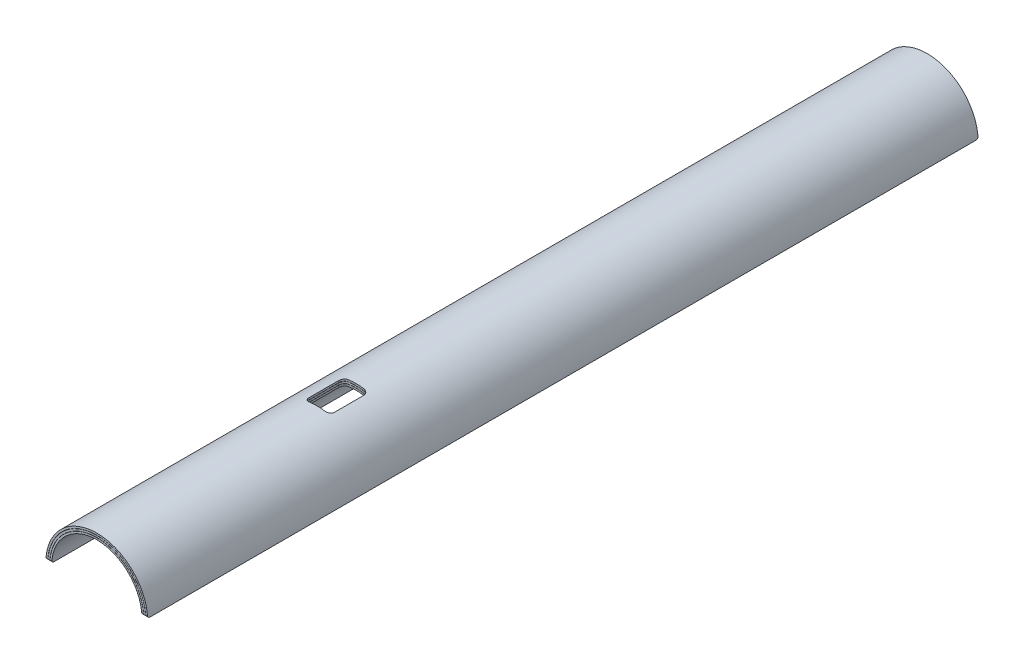
SolidWorks part; units mm, degrees
material "insulation"
ref_plane "Front Plane" through (0, 0, 0) normal (0, 0, 1) x (1, 0, 0)
ref_plane "Top Plane" through (0, 0, 0) normal (0, 1, 0) x (1, 0, 0)
ref_plane "Right Plane" through (0, 0, 0) normal (1, 0, 0) x (0, 0, -1)
sketch "Sketch1" plane through (0, 0, 0) normal (0, 0, 1) x (1, 0, 0)
  line L0 (-56.921, 3) -> (56.921, 3) construction
  line L1 (0, 0) -> (39.4027, 0) construction
  arc A0 (56.921, 3) -> (-56.921, 3) centre (0, 0) ccw
  dimension "D1" = 3
  dimension "D2" = 57
extrude "Extrude-Thin1" add sketch "Sketch1" along normal mid plane 1048 thin
sketch "Sketch2" plane through (0, 0, 0) normal (0, 0, 1) x (1, 0, 0)
  line L0 (-59.4443, 3) -> (59.4443, 3) construction
  line L1 (-56.921, 3) -> (56.921, 3) construction
  arc A0 (59.4443, 3) -> (-59.4443, 3) centre (0, 0) ccw
  dimension "D1" = 59.52
extrude "Extrude-Thin2" add sketch "Sketch2" along normal mid plane 1048 separate body thin
sketch "Sketch3" plane through (0, 0, 0) normal (0, 0, 1) x (1, 0, 0)
  line L0 (-61.9674, 3) -> (61.9674, 3) construction
  line L1 (-56.921, 3) -> (56.921, 3) construction
  arc A0 (61.9674, 3) -> (-61.9674, 3) centre (0, 0) ccw
  dimension "D1" = 62.04
extrude "Extrude-Thin3" add sketch "Sketch3" along normal mid plane 1048 separate body thin
fillet "Fillet1" radius 3 4 edges at (63.1161, 3.0556, 524) (63.1161, 3.0556, -524) (-63.1161, 3.0556, -524) (-63.1161, 3.0556, 524)
fillet "Fillet2" radius 3 4 edges at (60.5929, 3.058, -524) (-60.5929, 3.058, -524) (60.5929, 3.058, 524) (-60.5929, 3.058, 524)
fillet "Fillet3" radius 3 4 edges at (58.0694, 3.0605, 524) (-58.0694, 3.0605, 524) (58.0694, 3.0605, -524) (-58.0694, 3.0605, -524)
sketch "Sketch4" plane through (0, 0, 0) normal (0, 1, 0) x (1, 0, 0)
  line L0 (0, 0) -> (0, 89.1347) construction
  line L1 (9.9984, -246) -> (-9.9984, -246)
  line L2 (16, -239.9984) -> (16, -203.0016)
  line L3 (9.9984, -197) -> (-9.9984, -197)
  line L4 (-16, -239.9984) -> (-16, -203.0016)
  line L5 (16, -246) -> (-16, -197) construction
  line L6 (16, -197) -> (-16, -246) construction
  line L7 (0, 0) -> (-104.8045, 0) construction
  arc A0 (-16, -239.9984) -> (-9.9984, -246) centre (-9.9984, -239.9984) ccw
  arc A1 (-16, -203.0016) -> (-9.9984, -197) centre (-9.9984, -203.0016) cw
  arc A2 (9.9984, -197) -> (16, -203.0016) centre (9.9984, -203.0016) cw
  arc A3 (9.9984, -246) -> (16, -239.9984) centre (9.9984, -239.9984) ccw
  point P0 (0, -221.5)
  dimension "D4" = 6.0016
  dimension "D1" = 221.5
  dimension "D2" = 49
  dimension "D3" = 32
extrude "Cut-Extrude1" cut sketch "Sketch4" along normal through all
